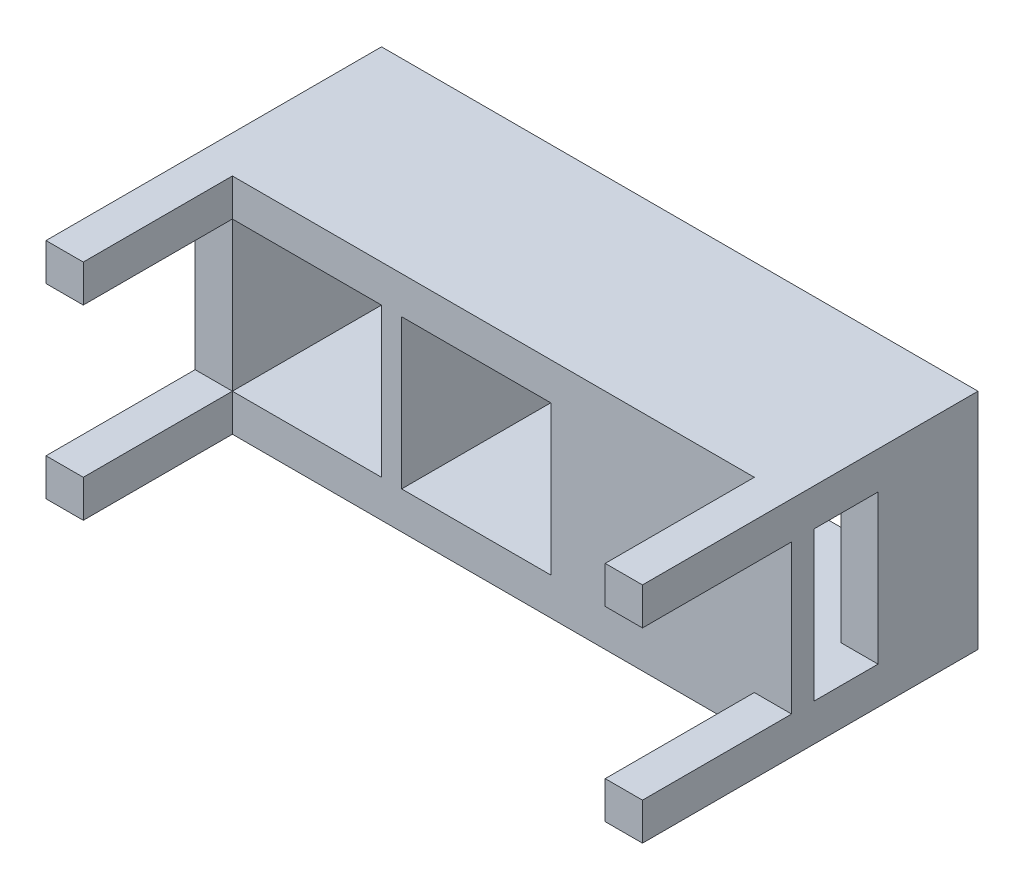
SolidWorks part; units mm, degrees
material "AISI 1010 Steel, hot rolled bar"
ref_plane "Front Plane" through (0, 0, 0) normal (0, 0, 1) x (1, 0, 0)
ref_plane "Top Plane" through (0, 0, 0) normal (0, 1, 0) x (1, 0, 0)
ref_plane "Right Plane" through (0, 0, 0) normal (1, 0, 0) x (0, 0, -1)
sketch "Sketch2" plane through (0, 0, 0) normal (0, 0, 1) x (1, 0, 0)
  line L1 (-347.0483, 131.3059) -> (452.9517, 131.3059)
  line L2 (-347.0483, 131.3059) -> (-347.0483, -168.6941)
  line L3 (-347.0483, -168.6941) -> (452.9517, -168.6941)
  line L4 (452.9517, 131.3059) -> (452.9517, -168.6941)
  dimension "D1" = 800
  dimension "D2" = 300
extrude "Boss-Extrude1" add sketch "Sketch2" along normal blind 100
sketch "Sketch3" plane through (0, 0, 100) normal (0, 0, 1) x (1, 0, 0)
  line L1 (-347.0483, 131.3059) -> (-297.0483, 131.3059)
  line L2 (-347.0483, 131.3059) -> (-347.0483, 81.3059)
  line L3 (-347.0483, 81.3059) -> (-297.0483, 81.3059)
  line L4 (-297.0483, 131.3059) -> (-297.0483, 81.3059)
  line L5 (-347.0483, -168.6941) -> (-297.0483, -168.6941)
  line L6 (-347.0483, -168.6941) -> (-347.0483, -118.6941)
  line L7 (-347.0483, -118.6941) -> (-297.0483, -118.6941)
  line L8 (-297.0483, -168.6941) -> (-297.0483, -118.6941)
  line L9 (452.9517, 131.3059) -> (402.9517, 131.3059)
  line L10 (452.9517, 131.3059) -> (452.9517, 81.3059)
  line L11 (452.9517, 81.3059) -> (402.9517, 81.3059)
  line L12 (402.9517, 131.3059) -> (402.9517, 81.3059)
  line L13 (452.9517, -168.6941) -> (402.9517, -168.6941)
  line L14 (452.9517, -168.6941) -> (452.9517, -118.6941)
  line L15 (452.9517, -118.6941) -> (402.9517, -118.6941)
  line L16 (402.9517, -168.6941) -> (402.9517, -118.6941)
  dimension "D1" = 50
  dimension "D2" = 50
  dimension "D3" = 50
  dimension "D4" = 50
  dimension "D5" = 50
  dimension "D6" = 50
  dimension "D7" = 50
  dimension "D8" = 50
extrude "Boss-Extrude2" add sketch "Sketch3" along normal blind 200
sketch "Sketch4" plane through (0, 0, 0) normal (0, 0, -1) x (-1, 0, 0)
  line L1 (-452.9517, 131.3059) -> (347.0483, 131.3059)
  line L2 (-452.9517, 131.3059) -> (-452.9517, -168.6941)
  line L3 (-452.9517, -168.6941) -> (347.0483, -168.6941)
  line L4 (347.0483, 131.3059) -> (347.0483, -168.6941)
  line L5 (-402.9517, 81.3059) -> (297.0483, 81.3059)
  line L6 (-402.9517, 81.3059) -> (-402.9517, -118.6941)
  line L7 (-402.9517, -118.6941) -> (297.0483, -118.6941)
  line L8 (297.0483, 81.3059) -> (297.0483, -118.6941)
  dimension "D1" = 50
  dimension "D2" = 50
  dimension "D3" = 50
  dimension "D4" = 50
extrude "Boss-Extrude3" add sketch "Sketch4" along normal blind 150
sketch "Sketch5" plane through (452.9517, 0, 0) normal (1, 0, 0) x (0, 0, -1)
  line L0 (-300, 131.3059) -> (150, 131.3059) construction
  line L1 (-70, 81.3059) -> (15.9544, 81.3059)
  line L2 (-70, 81.3059) -> (-70, -118.6941)
  line L3 (-70, -118.6941) -> (15.9544, -118.6941)
  line L4 (15.9544, 81.3059) -> (15.9544, -118.6941)
  line L5 (-300, -168.6941) -> (150, -168.6941) construction
  line L6 (-100, -118.6941) -> (-100, 81.3059) construction
  dimension "D1" = 50
  dimension "D2" = 50
  dimension "D3" = 30
extrude "Cut-Extrude1" cut sketch "Sketch5" against normal blind 750
sketch "Sketch6" plane through (0, 0, 70) normal (0, 0, -1) x (-1, 0, 0)
  line L0 (297.0483, 81.3059) -> (-402.9517, 81.3059) construction
  line L1 (297.0483, -118.6941) -> (297.0483, 81.3059) construction
  line L3 (70.0483, 81.3059) -> (77.0483, 81.3059)
  line L4 (70.0483, 81.3059) -> (70.0483, -118.6941)
  line L5 (70.0483, -118.6941) -> (77.0483, -118.6941)
  line L6 (77.0483, 81.3059) -> (77.0483, -118.6941)
  line L7 (297.0483, -118.6941) -> (-452.9517, -118.6941) construction
  point P10 (297.0483, -18.6941)
  dimension "D1" = 7
  dimension "D2" = 220
extrude "Boss-Extrude5" add sketch "Sketch6" along normal blind 185
sketch "Sketch9" plane through (0, 0, 70) normal (0, 0, -1) x (-1, 0, 0)
  line L0 (70.0483, 81.3059) -> (-452.9517, 81.3059) construction
  line L1 (-156.9517, 81.3059) -> (-149.9517, 81.3059)
  line L2 (-156.9517, 81.3059) -> (-156.9517, -111.6843)
  line L3 (-156.9517, -111.6843) -> (-149.9517, -111.6843)
  line L4 (-149.9517, 81.3059) -> (-149.9517, -111.6843)
  line L5 (70.0483, 81.3059) -> (70.0483, -118.6941) construction
  point P8 (70.0483, -18.6941)
  dimension "D1" = 7
  dimension "D2" = 220
extrude "Boss-Extrude6" add sketch "Sketch9" along normal blind 160
sketch "Sketch12" plane through (0, 0, 70) normal (0, 0, -1) x (-1, 0, 0)
  line L0 (297.0483, 81.3059) -> (77.0483, 81.3059) construction
  line L1 (97.0483, 81.3059) -> (297.0483, 81.3059)
  line L2 (97.0483, 81.3059) -> (97.0483, -118.6941)
  line L3 (97.0483, -118.6941) -> (297.0483, -118.6941)
  line L4 (297.0483, 81.3059) -> (297.0483, -118.6941)
  line L5 (77.0483, -118.6941) -> (77.0483, 81.3059) construction
  line L6 (70.0483, 81.3059) -> (-149.9517, 81.3059) construction
  line L7 (-129.9517, 81.3059) -> (70.0483, 81.3059)
  line L8 (-129.9517, 81.3059) -> (-129.9517, -118.6941)
  line L9 (-129.9517, -118.6941) -> (70.0483, -118.6941)
  line L10 (70.0483, 81.3059) -> (70.0483, -118.6941)
  line L11 (-149.9517, -111.6843) -> (-149.9517, 81.3059) construction
  dimension "D1" = 20
  dimension "D2" = 20
extrude "Cut-Extrude4" cut sketch "Sketch12" against normal blind 111
sketch "Sketch14" plane through (0, 0, 70) normal (0, 0, -1) x (-1, 0, 0)
  line L0 (-402.9517, -118.6941) -> (297.0483, -118.6941) construction
  line L1 (-156.9517, -111.6843) -> (-150.1418, -111.6843)
  line L2 (-156.9517, -111.6843) -> (-156.9517, -118.6941)
  line L3 (-156.9517, -118.6941) -> (-150.1418, -118.6941)
  line L4 (-150.1418, -111.6843) -> (-150.1418, -118.6941)
extrude "Boss-Extrude9" add sketch "Sketch14" along normal blind 160
sketch3d "3DSketch1"
  line L1 (-297.0483, 81.3059, -150) -> (-304.0483, 81.3059, -150)
  line L2 (-297.0483, 81.3059, -150) -> (-297.0483, 91.3059, -150)
  line L3 (-297.0483, 91.3059, -150) -> (-304.0483, 91.3059, -150)
  line L4 (-304.0483, 81.3059, -150) -> (-304.0483, 91.3059, -150)
  line L5 (-297.0483, -118.6941, -150) -> (-304.0483, -118.6941, -150)
  line L6 (-297.0483, -118.6941, -150) -> (-297.0483, -128.6941, -150)
  line L7 (-297.0483, -128.6941, -150) -> (-304.0483, -128.6941, -150)
  line L8 (-304.0483, -118.6941, -150) -> (-304.0483, -128.6941, -150)
  dimension "D1" = 7
  dimension "D2" = 10
  dimension "D3" = 7
  dimension "D4" = 10
extrude "Boss-Extrude10" add sketch "3DSketch1" along direction (0, 0, -1) on the side of the normal blind 7
sketch3d "3DSketch2"
  line L0 (-297.0483, -128.6941, -157) -> (-304.0483, -128.6941, -150)
  line L1 (-304.0483, -128.6941, -157) -> (-297.0483, -128.6941, -150)
  circle A0 centre (-300.5483, -128.6941, -153.5) radius 2.5
  point P10 (-300.5483, -126.1941, -153.5)
extrude "Cut-Extrude5" cut sketch "3DSketch2" along direction (0, 1, 0) on the side against the normal mid plane 527 contours A0
equation "\"f\"=1821"
